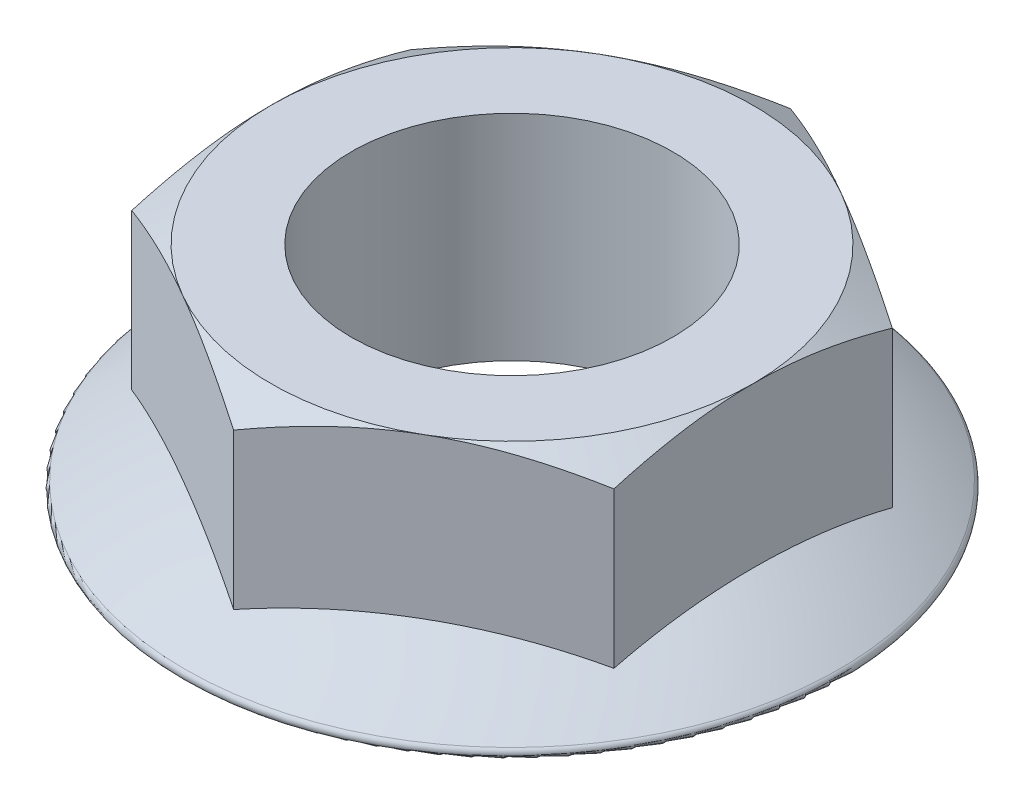
SolidWorks part; units mm, degrees
ref_plane "Front Plane" through (0, 0, 0) normal (0, 0, 1) x (1, 0, 0)
ref_plane "Top Plane" through (0, 0, 0) normal (0, 1, 0) x (1, 0, 0)
ref_plane "Right Plane" through (0, 0, 0) normal (1, 0, 0) x (0, 0, -1)
sketch "Sketch1" plane through (0, 0, 0) normal (0, 1, 0) x (1, 0, 0)
  line L1 (0, 25.9808) -> (-22.5, 12.9904)
  line L2 (-22.5, 12.9904) -> (-22.5, -12.9904)
  line L3 (-22.5, -12.9904) -> (0, -25.9808)
  line L4 (0, -25.9808) -> (22.5, -12.9904)
  line L5 (22.5, -12.9904) -> (22.5, 12.9904)
  line L6 (22.5, 12.9904) -> (0, 25.9808)
  circle A0 centre (0, 0) radius 22.5 construction
  dimension "D1" = 45
extrude "Boss-Extrude1" add sketch "Sketch1" along normal blind 20
sketch "Sketch3" plane through (0, 0, 0) normal (1, 0, 0) x (0, 0, -1)
  line L0 (0, 0) -> (0, 50000) construction
  line L1 (-15.4691, 0) -> (-50015.4691, 0) construction
  line L2 (-12.9904, 0) -> (12.9904, 0) construction
  line L3 (0, 9.6822) -> (0, 0)
  line L4 (0, 0) -> (31.95, 0)
  arc A0 (31.95, 0) -> (0, 9.6822) centre (0, -47.8746) ccw
  point P7 (0, 0)
  dimension "D2" = 57.5568
  dimension "D1" = 31.95
revolve "Revolve1" add sketch "Sketch3" angle 360 about L0
fillet "Fillet1" radius 0.5 1 edges at (0, 0, -31.95)
hole_wizard "Ø1.5mm Dowel Hole1" positions "Sketch4" profile "Sketch5" hole size "Ø1.5" standard "ANSI Metric" end condition up to next
sketch "Sketch4" plane through (0, 20, 0) normal (0, 1, 0) x (1, 0, 0)
  point P0 (0, 0)
sketch "Sketch5" plane through (0, 20, 0) normal (1, 0, 0) x (0, 0, 1)
  line L0 (0, 0) -> (0, 20)
  line L1 (0, 20) -> (15, 20)
  line L2 (15, 20) -> (15, 0)
  line L5 (15, 0) -> (0, 0)
  line L11 (0, -6.35) -> (0, 107.95) construction
  dimension "Thru Hole Dia." = 30
  dimension "Thru Hole Depth" = 20
cosmetic thread "Cosmetic Thread1" parameters "D2"=33
sketch "Sketch6" plane through (0, 0, 0) normal (0, 0, 1) x (1, 0, 0)
  line L0 (0, 0) -> (0, 50000) construction
  line L1 (22.5, 20) -> (28.5, 20)
  line L2 (28.5, 20) -> (28.5, 16.5359)
  line L3 (28.5, 16.5359) -> (22.5, 20)
  dimension "D1" = 30
  dimension "D2" = 6
revolve "Cut-Revolve1" cut sketch "Sketch6" angle 360 about L0
